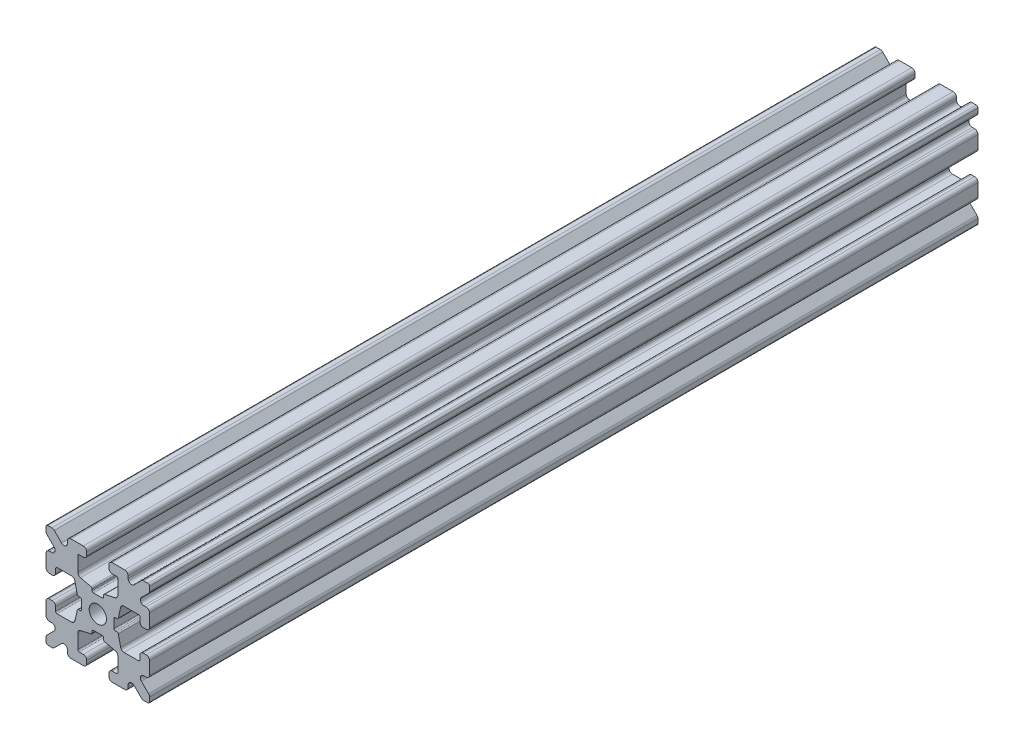
SolidWorks part; units mm, degrees
ref_plane "Front Plane" through (0, 0, 0) normal (0, 0, 1) x (1, 0, 0)
ref_plane "Top Plane" through (0, 0, 0) normal (0, 1, 0) x (1, 0, 0)
ref_plane "Right Plane" through (0, 0, 0) normal (1, 0, 0) x (0, 0, -1)
sketch "Sketch1" plane through (0, 0, 0) normal (0, 0, 1) x (1, 0, 0)
  line L1 (-7.5, -7.5) -> (7.5, -7.5)
  line L2 (-7.5, -7.5) -> (-7.5, 7.5)
  line L3 (-7.5, 7.5) -> (7.5, 7.5)
  line L4 (7.5, -7.5) -> (7.5, 7.5)
  line L5 (-7.5, -7.5) -> (7.5, 7.5) construction
  line L6 (-7.5, 7.5) -> (7.5, -7.5) construction
  circle A0 centre (0, 0) radius 1.25
  point P0 (0, 0)
  dimension "D2" = 2.5
  dimension "D1" = 15
extrude "Boss-Extrude1" add sketch "Sketch1" along normal mid plane 120
fillet "Fillet1" radius 0.25 4 edges at (7.5, -7.5, 0) (-7.5, -7.5, 0) (7.5, 7.5, 0) (-7.5, 7.5, 0)
sketch "Sketch2" plane through (0, 0, 60) normal (0, 0, 1) x (1, 0, 0)
  line L0 (-7.5, 7.25) -> (-7.5, -7.25) construction
  line L1 (-7.5, 1.6) -> (-6.1, 1.6)
  line L2 (-7.5, 1.6) -> (-7.5, -1.6)
  line L3 (-7.5, -1.6) -> (-6.1, -1.6)
  line L4 (-6.1, 1.6) -> (-6.1, 2.9)
  line L5 (0, 0) -> (-12.1036, 0) construction
  line L6 (-6.1, -2.9) -> (-3.4, -2.9)
  line L7 (0, 0) -> (-7.25, 7.25) construction
  line L8 (-6.1, 2.9) -> (-3.4, 2.9)
  line L9 (-3.4, -2.9) -> (-3.4, 2.9)
  line L10 (55, 0) -> (-55, 0) construction
  line L11 (-6.1, -2.9) -> (-6.1, -1.6)
  line L12 (2.9, 6.1) -> (1.6, 6.1)
  line L13 (2.9, 3.4) -> (-2.9, 3.4)
  line L14 (-2.9, 6.1) -> (-2.9, 3.4)
  line L15 (2.9, 6.1) -> (2.9, 3.4)
  line L16 (-1.6, 6.1) -> (-2.9, 6.1)
  line L17 (1.6, 7.5) -> (1.6, 6.1)
  line L18 (-1.6, 7.5) -> (1.6, 7.5)
  line L19 (-1.6, 7.5) -> (-1.6, 6.1)
  line L20 (-1.6, -7.5) -> (-1.6, -6.1)
  line L21 (-1.6, -7.5) -> (1.6, -7.5)
  line L22 (1.6, -7.5) -> (1.6, -6.1)
  line L23 (-1.6, -6.1) -> (-2.9, -6.1)
  line L24 (2.9, -6.1) -> (2.9, -3.4)
  line L25 (-2.9, -6.1) -> (-2.9, -3.4)
  line L26 (2.9, -3.4) -> (-2.9, -3.4)
  line L27 (2.9, -6.1) -> (1.6, -6.1)
  line L28 (6.1, -2.9) -> (6.1, -1.6)
  line L29 (3.4, -2.9) -> (3.4, 2.9)
  line L30 (6.1, 2.9) -> (3.4, 2.9)
  line L31 (6.1, -2.9) -> (3.4, -2.9)
  line L32 (6.1, 1.6) -> (6.1, 2.9)
  line L33 (7.5, -1.6) -> (6.1, -1.6)
  line L34 (7.5, 1.6) -> (7.5, -1.6)
  line L35 (7.5, 1.6) -> (6.1, 1.6)
  dimension "D1" = 3.2
  dimension "D2" = 5.8
  dimension "D3" = 1.4
  dimension "D4" = 2.7
extrude "Cut-Extrude1" cut sketch "Sketch2" against normal through all
sketch "Sketch4" plane through (0, 0, 60) normal (0, 0, 1) x (1, 0, 0)
  line L0 (-3.4, 2.9) -> (-2.75, 0)
  line L1 (55, 0) -> (-55, 0) construction
  line L2 (-2.75, 0) -> (-3.4, -2.9)
  line L3 (-3.4, -2.9) -> (-3.4, 2.9) construction
  line L4 (-3.4, 2.9) -> (-3.4, -2.9)
  line L5 (-2.9, 3.4) -> (0, 2.75)
  line L6 (0, 2.75) -> (2.9, 3.4)
  line L7 (2.9, 3.4) -> (-2.9, 3.4)
  line L8 (3.4, 2.9) -> (2.75, 0)
  line L9 (2.75, 0) -> (3.4, -2.9)
  line L10 (3.4, -2.9) -> (3.4, 2.9)
  line L11 (-2.9, -3.4) -> (0, -2.75)
  line L12 (0, -2.75) -> (2.9, -3.4)
  line L13 (2.9, -3.4) -> (-2.9, -3.4)
  circle A2 centre (0, 0) radius 2.75
  circle A3 centre (0, 0) radius 2.75 construction
  dimension "D1" = 1.5
extrude "Cut-Extrude3" cut sketch "Sketch4" against normal through all
fillet "Fillet3" radius 0.5 16 edges at (-6.1, -1.6, 0) (-7.5, -1.6, 0) (-6.1, 1.6, 0) (-7.5, 1.6, 0) (-1.6, -7.5, 0) (-1.6, -6.1, 0) (1.6, -7.5, 0) (1.6, -6.1, 0) (6.1, -1.6, 0) (7.5, -1.6, 0) (7.5, 1.6, 0) (6.1, 1.6, 0) (1.6, 7.5, 0) (1.6, 6.1, 0) (-1.6, 7.5, 0) (-1.6, 6.1, 0)
fillet "Fillet4" radius 0.5 8 edges at (-3.4, 2.9, 0) (-3.4, -2.9, 0) (2.9, -3.4, 0) (-2.9, -3.4, 0) (3.4, -2.9, 0) (3.4, 2.9, 0) (-2.9, 3.4, 0) (2.9, 3.4, 0)
fillet "Fillet5" radius 3 4 edges at (0, -2.75, 0) (2.75, 0, 0) (-2.75, 0, 0) (0, 2.75, 0)
fillet "Fillet6" radius 0.2 8 edges at (-2.9, -6.1, 0) (2.9, -6.1, 0) (6.1, -2.9, 0) (6.1, 2.9, 0) (2.9, 6.1, 0) (-2.9, 6.1, 0) (-6.1, -2.9, 0) (-6.1, 2.9, 0)
sketch "Sketch5" plane through (0, 0, 60) normal (0, 0, 1) x (1, 0, 0)
  line L0 (0, 0) -> (-7.25, 7.25) construction
  line L1 (-7.5, 6.4393) -> (-5.4607, 4.4)
  line L2 (-6.4393, 7.5) -> (-4.4, 5.4607)
  line L3 (-7.5, 4.4) -> (-5.4607, 4.4)
  line L4 (-3.8003, 2.9) -> (-5.9, 2.9) construction
  line L5 (0, 0) -> (-12.1819, 0) construction
  line L6 (-4.4, 7.5) -> (-4.4, 5.4607)
  line L7 (-2.9, 5.9) -> (-2.9, 3.8003) construction
  line L8 (-7.5, 6.4393) -> (-7.5, 4.4)
  line L9 (-7.5, 7.25) -> (-7.5, 2.1) construction
  line L10 (2.1, -7.5) -> (7.25, -7.5) construction
  line L11 (7.5, -7.25) -> (7.5, -2.1) construction
  line L12 (7.25, 7.5) -> (2.1, 7.5) construction
  line L13 (-2.1, 7.5) -> (-7.25, 7.5) construction
  line L14 (-4.4, 7.5) -> (-6.4393, 7.5)
  line L16 (55, 0) -> (-55, 0) construction
  line L17 (0, 0) -> (0, 10.993) construction
  line L18 (0, -54.6431) -> (0, 54.6431) construction
  line L20 (4.4, 7.5) -> (6.4393, 7.5)
  line L22 (7.5, 6.4393) -> (7.5, 4.4)
  line L23 (4.4, 7.5) -> (4.4, 5.4607)
  line L24 (7.5, 4.4) -> (5.4607, 4.4)
  line L25 (6.4393, 7.5) -> (4.4, 5.4607)
  line L26 (7.5, 6.4393) -> (5.4607, 4.4)
  line L27 (7.5, -6.4393) -> (5.4607, -4.4)
  line L28 (6.4393, -7.5) -> (4.4, -5.4607)
  line L29 (7.5, -4.4) -> (5.4607, -4.4)
  line L30 (4.4, -7.5) -> (4.4, -5.4607)
  line L31 (7.5, -6.4393) -> (7.5, -4.4)
  line L33 (4.4, -7.5) -> (6.4393, -7.5)
  line L36 (-4.4, -7.5) -> (-6.4393, -7.5)
  line L38 (-7.5, -6.4393) -> (-7.5, -4.4)
  line L39 (-4.4, -7.5) -> (-4.4, -5.4607)
  line L40 (-7.5, -4.4) -> (-5.4607, -4.4)
  line L41 (-6.4393, -7.5) -> (-4.4, -5.4607)
  line L42 (-7.5, -6.4393) -> (-5.4607, -4.4)
  dimension "D1" = 1.5
  dimension "D2" = 1.5
  dimension "D3" = 1.5
extrude "Cut-Extrude4" cut sketch "Sketch5" against normal through all
fillet "Fillet8" radius 0.5 24 edges at (-5.4607, 4.4, 0) (-7.5, 4.4, 0) (-5.4607, -4.4, 0) (-7.5, -4.4, 0) (-4.4, -7.5, 0) (-4.4, -5.4607, 0) (4.4, -7.5, 0) (4.4, -5.4607, 0) (5.4607, -4.4, 0) (7.5, -4.4, 0) (7.5, 4.4, 0) (5.4607, 4.4, 0) (4.4, 5.4607, 0) (4.4, 7.5, 0) (-4.4, 5.4607, 0) (-4.4, 7.5, 0) (-6.4393, 7.5, 0) (-7.5, 6.4393, 0) (6.4393, 7.5, 0) (7.5, 6.4393, 0) (6.4393, -7.5, 0) (7.5, -6.4393, 0) (-6.4393, -7.5, 0) (-7.5, -6.4393, 0)
sketch "Sketch6" plane through (0, 0, 60) normal (0, 0, 1) x (1, 0, 0)
  line L0 (0, 0) -> (0, 11.013) construction
  line L1 (0.6561, 2.8971) -> (2.1235, 2.8971) construction
  line L2 (0, -54.6431) -> (0, 54.6431) construction
  line L3 (0, 0) -> (7.25, 7.25) construction
  line L4 (7.5, 0.8255) -> (7.5, -0.8255)
  line L5 (2.3471, 0.8255) -> (7.5, 0.8255)
  line L6 (0, 0) -> (12.4016, 0) construction
  line L7 (0.8255, -7.5) -> (-0.8255, -7.5)
  line L8 (2.3471, -0.8255) -> (2.3471, 0.8255)
  line L9 (0.8255, -2.3471) -> (0.8255, -7.5)
  line L10 (7.5, -0.8255) -> (2.3471, -0.8255)
  line L11 (-7.5, -0.8255) -> (-2.3471, -0.8255)
  line L12 (-2.3471, -0.8255) -> (-2.3471, 0.8255)
  line L13 (-0.8255, -2.3471) -> (0.8255, -2.3471)
  line L14 (-0.8255, 7.5) -> (-0.8255, 2.3471)
  line L15 (-0.8255, 2.3471) -> (0.8255, 2.3471)
  line L16 (-0.8255, -7.5) -> (-0.8255, -2.3471)
  line L17 (0.8255, 2.3471) -> (0.8255, 7.5)
  line L18 (0.8255, 7.5) -> (-0.8255, 7.5)
  line L19 (3.9, 7.5) -> (2.1, 7.5) construction
  line L20 (-2.3471, 0.8255) -> (-7.5, 0.8255)
  line L21 (-7.5, 0.8255) -> (-7.5, -0.8255)
  point P5 (0, -2.5973)
  point P7 (0, 2.5973)
  dimension "D3" = 0.55
  dimension "D1" = 1.651
extrude "Cut-Extrude5" cut sketch "Sketch6" against normal through all
fillet "Fillet10" radius 0.2 16 edges at (-2.935, 0.8255, 0) (-2.935, -0.8255, 0) (2.935, -0.8255, 0) (2.935, 0.8255, 0) (0.8255, 2.935, 0) (-0.8255, 2.935, 0) (-2.3471, 0.8255, 0) (-2.3471, -0.8255, 0) (0.8255, 2.3471, 0) (-0.8255, 2.3471, 0) (2.3471, 0.8255, 0) (2.3471, -0.8255, 0) (0.8255, -2.935, 0) (0.8255, -2.3471, 0) (-0.8255, -2.3471, 0) (-0.8255, -2.935, 0)
